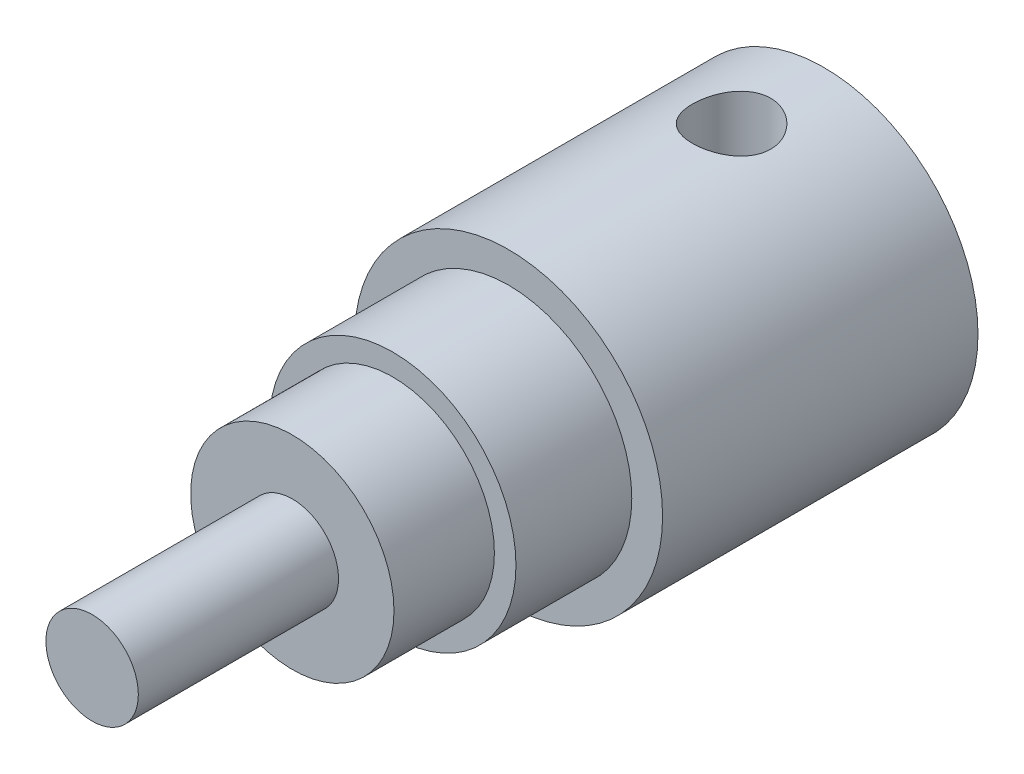
SolidWorks part; units mm, degrees
ref_plane "Plan de face" through (0, 0, 0) normal (0, 0, 1) x (1, 0, 0)
ref_plane "Plan de dessus" through (0, 0, 0) normal (0, 1, 0) x (1, 0, 0)
ref_plane "Plan de droite" through (0, 0, 0) normal (1, 0, 0) x (0, 0, -1)
sketch "Esquisse1" plane through (0, 0, 0) normal (0, 0, 1) x (1, 0, 0)
  circle A0 centre (0, 0) radius 25
extrude "Boss.-Extru.1" add sketch "Esquisse1" along normal blind 51.2
sketch "Esquisse2" plane through (0, 0, 51.2) normal (0, 0, 1) x (1, 0, 0)
  circle A0 centre (0, 0) radius 20
extrude "Boss.-Extru.2" add sketch "Esquisse2" along normal blind 18.8
sketch "Esquisse3" plane through (0, 0, 70) normal (0, 0, 1) x (1, 0, 0)
  circle A0 centre (0, 0) radius 16.5
extrude "Boss.-Extru.3" add sketch "Esquisse3" along normal blind 16.7
sketch "Esquisse4" plane through (0, 0, 86.7) normal (0, 0, 1) x (1, 0, 0)
  circle A0 centre (0, 0) radius 27.5
extrude "Boss.-Extru.4" add sketch "Esquisse4" along normal blind 47.1
chamfer "Chanfrein1" distance 10 angle 60 1 edges at (27.5, 0, 86.7)
sketch "Esquisse12" plane through (0, 0, 0) normal (0, 1, 0) x (1, 0, 0)
  line L0 (0, -27.5) -> (0, 27.5) construction
  line L1 (-27.5, 0) -> (27.5, 0) construction
  circle A0 centre (0, -15) radius 6.35
  point P0 (0, -15)
  dimension "D1" = 15
extrude "Enlèv. mat.-Extru.1" cut sketch "Esquisse12" against normal through all both and the other way through all
sketch "Esquisse13" plane through (0, 0, 133.8) normal (0, 0, 1) x (1, 0, 0)
  line L0 (27.5, 0) -> (-27.5, 0) construction
  circle A0 centre (0.544, 0) radius 47.2584
extrude "Enlèv. mat.-Extru.2" cut sketch "Esquisse13" against normal blind 15 contours A0
sketch "Esquisse14" plane through (0, 0, 118.8) normal (0, 0, 1) x (1, 0, 0)
  circle A0 centre (0, 0) radius 7.5
  circle A1 centre (0, 0) radius 39.9347
  dimension "15" = 15
extrude "Enlèv. mat.-Extru.4" cut sketch "Esquisse14" against normal blind 32.5 contours A0 | A1
